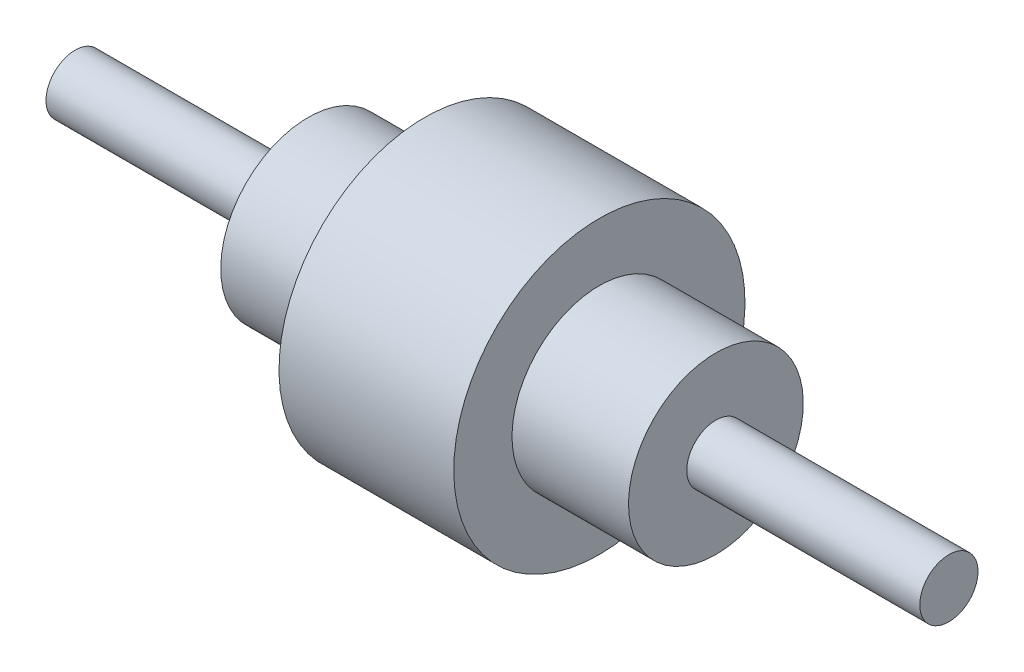
SolidWorks part; units mm, degrees
ref_plane "Front Plane" through (0, 0, 0) normal (0, 0, 1) x (1, 0, 0)
ref_plane "Top Plane" through (0, 0, 0) normal (0, 1, 0) x (1, 0, 0)
ref_plane "Right Plane" through (0, 0, 0) normal (1, 0, 0) x (0, 0, -1)
sketch "Sketch1" plane through (0, 0, 0) normal (0, 0, 1) x (1, 0, 0)
  line L0 (-337.1967, 0) -> (241.9948, 0) construction
  line L1 (80, -10) -> (80, 0)
  line L2 (80, 0) -> (-220, 0)
  line L3 (0, -10) -> (80, -10)
  line L6 (0, -10) -> (0, -30)
  line L7 (0, -30) -> (-40, -30)
  line L10 (-40, -30) -> (-40, -50)
  line L11 (-40, -50) -> (-100, -50)
  line L12 (-100, -30) -> (-100, -50)
  line L15 (-100, -30) -> (-140, -30)
  line L16 (-140, -10) -> (-140, -30)
  line L19 (-140, -10) -> (-220, -10)
  line L20 (-220, 0) -> (-220, -10)
  dimension "D1" = 80
  dimension "D3" = 40
  dimension "D4" = 60
  dimension "D6" = 40
  dimension "D7" = 80
revolve "Revolve6" add sketch "Sketch1" angle 360 about L0
